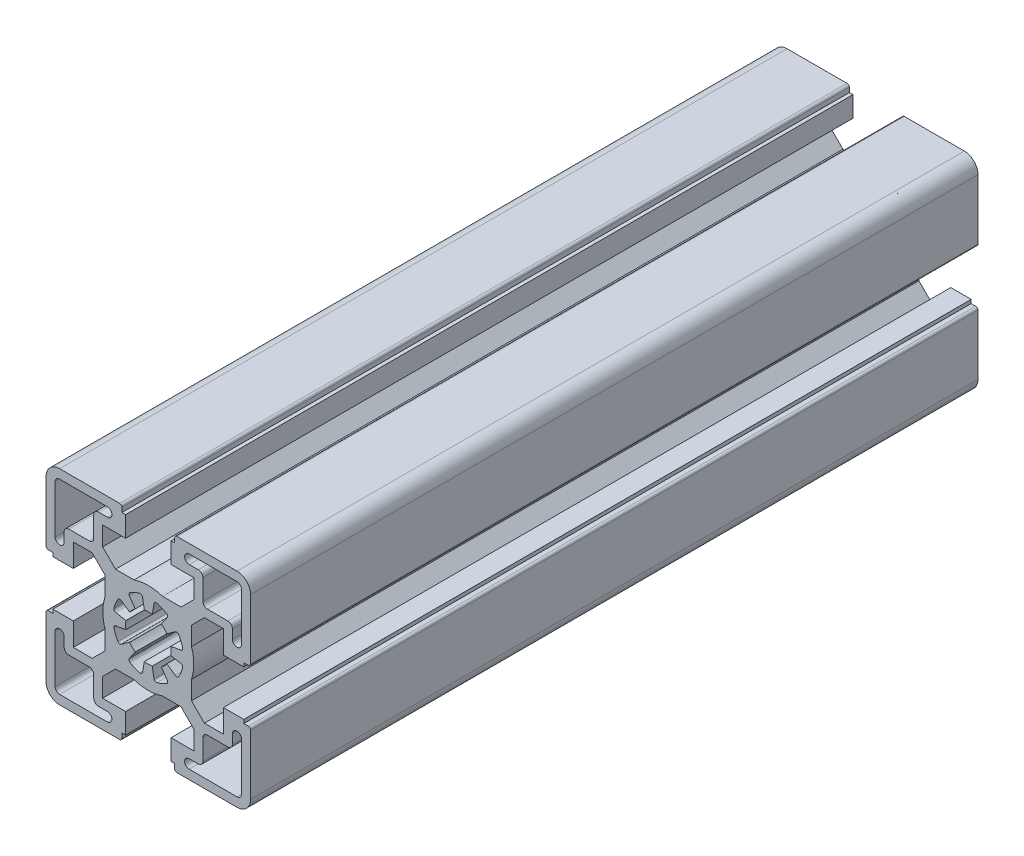
SolidWorks part; units mm, degrees
material "АД31 ГОСТ 4784-97"
ref_plane "Front Plane" through (0, 0, 0) normal (0, 0, 1) x (1, 0, 0)
ref_plane "Top Plane" through (0, 0, 0) normal (0, 1, 0) x (1, 0, 0)
ref_plane "Right Plane" through (0, 0, 0) normal (1, 0, 0) x (0, 0, -1)
sketch "Sketch1" plane through (0, 0, 0) normal (0, 0, 1) x (1, 0, 0)
  line L0 (0, 34.901) -> (0, -38.8683) construction
  line L1 (-27.7848, 0) -> (42.6814, 0) construction
  line L3 (2.8679, -4.0957) -> (4.1737, -5.9606)
  line L4 (-4.1737, -5.9606) -> (-2.8679, -4.0957)
  line L5 (-0.8682, -4.924) -> (-1.2635, -7.166)
  line L6 (0.8682, -4.924) -> (1.2636, -7.166)
  line L7 (4.0957, -2.8679) -> (5.9606, -4.1736)
  line L8 (4.924, -0.8682) -> (7.166, -1.2636)
  line L9 (-7.166, -1.2636) -> (-4.924, -0.8682)
  line L10 (-4.0957, -2.8679) -> (-5.9606, -4.1736)
  line L88 (0.8682, 4.924) -> (1.2636, 7.166)
  line L89 (-0.8682, 4.924) -> (-1.2635, 7.166)
  line L90 (-4.1737, 5.9606) -> (-2.8679, 4.0957)
  line L91 (-4.0957, 2.8679) -> (-5.9606, 4.1736)
  line L92 (-7.166, 1.2636) -> (-4.924, 0.8682)
  line L101 (4.924, 0.8682) -> (7.166, 1.2636)
  line L102 (4.0957, 2.8679) -> (5.9606, 4.1736)
  line L103 (2.8679, 4.0957) -> (4.1737, 5.9606)
  line L104 (-5, -16.4999) -> (-5, -20.9999)
  line L105 (-5, -20.9999) -> (-5.8, -20.9999)
  line L106 (-5.8, -20.9999) -> (-5.8, -22)
  line L107 (-6.3, -22.5) -> (-19.5, -22.5)
  line L108 (-22.5, -19.5) -> (-22.5, -6.2999)
  line L109 (-22, -5.7999) -> (-21, -5.7999)
  line L110 (-21, -5.7999) -> (-21, -4.9999)
  line L111 (-21, -4.9999) -> (-16.5, -4.9999)
  line L112 (-16.5, -4.9999) -> (-16.5, -10.0499)
  line L113 (-16.5, -10.0499) -> (-12.3429, -10.0499)
  line L114 (-12.3429, -10.0499) -> (-9.5, -7.207)
  line L115 (-9.5, -7.207) -> (-9.5, -3.1226)
  line L116 (-9.5, 3.1227) -> (-9.5, 7.207)
  line L117 (-9.5, 7.207) -> (-12.3429, 10.0499)
  line L118 (-12.3429, 10.0499) -> (-16.5, 10.0499)
  line L119 (-16.5, 10.0499) -> (-16.5, 4.9999)
  line L120 (-16.5, 4.9999) -> (-21, 4.9999)
  line L121 (-21, 4.9999) -> (-21, 5.7999)
  line L122 (-21, 5.7999) -> (-22, 5.7999)
  line L123 (-22.5, 6.2999) -> (-22.5, 19.5)
  line L124 (-19.5, 22.5) -> (-6.3, 22.5)
  line L125 (-5.7999, 21.9999) -> (-5.7999, 20.9999)
  line L126 (-5.7999, 20.9999) -> (-5, 20.9999)
  line L127 (-5, 20.9999) -> (-5, 16.5)
  line L128 (-5, 16.5) -> (-10.0501, 16.5)
  line L129 (-10.0501, 16.5) -> (-10.0501, 12.3428)
  line L130 (-10.0501, 12.3428) -> (-7.2072, 9.4999)
  line L131 (-7.2072, 9.4999) -> (-3.1228, 9.4999)
  line L132 (3.1226, 9.4999) -> (7.207, 9.4999)
  line L133 (7.207, 9.4999) -> (10.0499, 12.3428)
  line L134 (10.0499, 12.3428) -> (10.0499, 16.5)
  line L135 (10.0499, 16.5) -> (5, 16.5)
  line L136 (5, 16.5) -> (5, 21)
  line L137 (5, 21) -> (5.7999, 21)
  line L138 (5.7999, 21) -> (5.7999, 21.9999)
  line L139 (6.3, 22.5) -> (19.5001, 22.5)
  line L140 (22.5001, 6.2999) -> (22.5001, 19.5)
  line L141 (22.0001, 5.7999) -> (21, 5.7999)
  line L142 (21, 5.7999) -> (21, 4.9999)
  line L143 (21, 4.9999) -> (16.5, 4.9999)
  line L144 (16.5, 4.9999) -> (16.5, 10.0499)
  line L145 (16.5, 10.0499) -> (12.3429, 10.0499)
  line L146 (12.3429, 10.0499) -> (9.4999, 7.207)
  line L147 (9.4999, 7.207) -> (9.4999, 3.1227)
  line L148 (9.4999, -3.1226) -> (9.4999, -7.207)
  line L149 (9.4999, -7.207) -> (12.3429, -10.0499)
  line L150 (12.3429, -10.0499) -> (16.5, -10.0499)
  line L151 (16.5, -10.0499) -> (16.5, -4.9999)
  line L152 (16.5, -4.9999) -> (21, -4.9999)
  line L153 (21, -4.9999) -> (21, -5.7999)
  line L154 (21, -5.7999) -> (22.0001, -5.7999)
  line L155 (22.5001, -6.2999) -> (22.5001, -19.5)
  line L156 (6.3, -22.5) -> (19.5001, -22.5)
  line L157 (5.8, -22) -> (5.8, -20.9999)
  line L158 (5.8, -20.9999) -> (5, -20.9999)
  line L159 (5, -20.9999) -> (5, -16.4999)
  line L160 (5, -16.4999) -> (10.0499, -16.4999)
  line L161 (10.0499, -16.4999) -> (10.0499, -12.3428)
  line L162 (10.0499, -12.3428) -> (7.2069, -9.4998)
  line L163 (7.2069, -9.4998) -> (3.1226, -9.4998)
  line L164 (-3.1228, -9.4998) -> (-7.2071, -9.4998)
  line L165 (-7.2071, -9.4998) -> (-10.0501, -12.3428)
  line L166 (-10.0501, -12.3428) -> (-10.0501, -16.4999)
  line L167 (-10.0501, -16.4999) -> (-5, -16.4999)
  line L168 (-17.5001, -12) -> (-13.0001, -12)
  line L169 (-12.0001, -17.4999) -> (-12.0001, -13)
  line L170 (-11.0001, -18.4999) -> (-9.0001, -18.4999)
  line L171 (-19.5001, -20.5) -> (-9.0001, -20.5)
  line L172 (-20.5001, -19.5) -> (-20.5001, -8.9999)
  line L173 (-18.5001, -11) -> (-18.5001, -8.9999)
  line L174 (13, -12) -> (17.5, -12)
  line L175 (12, -17.4999) -> (12, -13)
  line L176 (9, -18.4999) -> (11, -18.4999)
  line L177 (9, -20.5) -> (19.5, -20.5)
  line L178 (20.5, -19.5) -> (20.5, -9.0001)
  line L179 (18.5, -11) -> (18.5, -9.0001)
  line L180 (-17.5001, 12) -> (-13.0001, 12)
  line L181 (-12.0001, 13) -> (-12.0001, 17.4999)
  line L182 (-11.0001, 18.4999) -> (-9.0001, 18.4999)
  line L183 (-19.5001, 20.5) -> (-9.0001, 20.5)
  line L184 (-20.5001, 8.9999) -> (-20.5001, 19.5)
  line L185 (-18.5001, 8.9999) -> (-18.5001, 11)
  line L186 (13, 12) -> (17.5, 12)
  line L187 (12, 13) -> (12, 17.4999)
  line L188 (9, 18.4999) -> (11, 18.4999)
  line L189 (9, 20.5) -> (19.5, 20.5)
  line L190 (20.5, 9.0001) -> (20.5, 19.5)
  line L191 (18.5, 9.0001) -> (18.5, 11)
  arc A0 (4.0221, -6.6756) -> (1.8763, -7.5644) centre (0, 0) cw
  arc A1 (-1.8763, -7.5645) -> (-4.0221, -6.6756) centre (0, 0) cw
  arc A2 (7.5644, -1.8763) -> (7.166, -1.2636) centre (7.0792, -1.756) ccw
  arc A3 (6.6756, -4.0221) -> (5.9606, -4.1736) centre (6.2474, -3.7641) cw
  arc A4 (4.0221, -6.6756) -> (4.1737, -5.9606) centre (3.7641, -6.2474) ccw
  arc A5 (1.8763, -7.5644) -> (1.2636, -7.166) centre (1.756, -7.0792) cw
  arc A6 (4.0957, -2.8679) -> (2.8679, -4.0957) centre (0, 0) cw
  arc A7 (7.5644, -1.8763) -> (6.6756, -4.0221) centre (0, 0) cw
  arc A8 (-1.8763, -7.5645) -> (-1.2635, -7.166) centre (-1.7559, -7.0792) ccw
  arc A9 (-4.0221, -6.6756) -> (-4.1737, -5.9606) centre (-3.7641, -6.2474) cw
  arc A10 (-6.6756, -4.0221) -> (-5.9606, -4.1736) centre (-6.2474, -3.7641) ccw
  arc A11 (-7.5644, -1.8763) -> (-7.166, -1.2636) centre (-7.0792, -1.756) cw
  arc A12 (7.166, 1.2636) -> (7.5644, 1.8763) centre (7.0792, 1.756) ccw
  arc A13 (6.6756, 4.0221) -> (5.9606, 4.1736) centre (6.2474, 3.7641) ccw
  arc A14 (4.1737, 5.9606) -> (4.0221, 6.6756) centre (3.7641, 6.2474) ccw
  arc A15 (1.8763, 7.5644) -> (1.2636, 7.166) centre (1.756, 7.0792) ccw
  arc A16 (-6.6756, -4.0221) -> (-7.5644, -1.8763) centre (0, 0) cw
  arc A17 (-2.8679, -4.0957) -> (-4.0957, -2.8679) centre (0, 0) cw
  arc A18 (0.8682, -4.924) -> (-0.8682, -4.924) centre (0, 0) cw
  arc A19 (-1.2635, 7.166) -> (-1.8763, 7.5645) centre (-1.7559, 7.0792) ccw
  arc A20 (-4.0221, 6.6756) -> (-4.1737, 5.9606) centre (-3.7641, 6.2474) ccw
  arc A21 (-7.166, 1.2636) -> (-7.5644, 1.8763) centre (-7.0792, 1.756) cw
  arc A22 (-6.6756, 4.0221) -> (-5.9606, 4.1736) centre (-6.2474, 3.7641) cw
  arc A56 (0.8682, 4.924) -> (-0.8682, 4.924) centre (0, 0) ccw
  arc A57 (-1.8763, 7.5645) -> (-4.0221, 6.6756) centre (0, 0) ccw
  arc A58 (-2.8679, 4.0957) -> (-4.0957, 2.8679) centre (0, 0) ccw
  arc A59 (-6.6756, 4.0221) -> (-7.5644, 1.8763) centre (0, 0) ccw
  arc A60 (-4.924, 0.8682) -> (-4.924, -0.8682) centre (0, 0) ccw
  arc A68 (4.924, -0.8682) -> (4.924, 0.8682) centre (0, 0) ccw
  arc A69 (7.5644, 1.8763) -> (6.6756, 4.0221) centre (0, 0) ccw
  arc A70 (4.0957, 2.8679) -> (2.8679, 4.0957) centre (0, 0) ccw
  arc A71 (4.0221, 6.6756) -> (1.8763, 7.5644) centre (0, 0) ccw
  arc A72 (-6.3, -22.5) -> (-5.8, -22) centre (-6.3, -22) ccw
  arc A73 (-22.5, -19.5) -> (-19.5, -22.5) centre (-19.5, -19.5) ccw
  arc A74 (-22, -5.7999) -> (-22.5, -6.2999) centre (-22, -6.2999) ccw
  arc A75 (-9.5, 3.1227) -> (-9.5, -3.1226) centre (0, 0.0001) ccw
  arc A76 (-22.5, 6.2999) -> (-22, 5.7999) centre (-22, 6.2999) ccw
  arc A77 (-19.5, 22.5) -> (-22.5, 19.5) centre (-19.5, 19.5) ccw
  arc A78 (-5.7999, 21.9999) -> (-6.3, 22.5) centre (-6.3, 21.9999) ccw
  arc A79 (3.1226, 9.4999) -> (-3.1228, 9.4999) centre (-0.0001, -0.0001) ccw
  arc A80 (6.3, 22.5) -> (5.7999, 21.9999) centre (6.3, 21.9999) ccw
  arc A81 (22.5001, 19.5) -> (19.5001, 22.5) centre (19.5001, 19.5) ccw
  arc A82 (22.0001, 5.7999) -> (22.5001, 6.2999) centre (22.0001, 6.2999) ccw
  arc A83 (9.4999, -3.1226) -> (9.4999, 3.1227) centre (0, 0.0001) ccw
  arc A84 (22.5001, -6.2999) -> (22.0001, -5.7999) centre (22.0001, -6.2999) ccw
  arc A85 (19.5001, -22.5) -> (22.5001, -19.5) centre (19.5001, -19.5) ccw
  arc A86 (5.8, -22) -> (6.3, -22.5) centre (6.3, -22) ccw
  arc A87 (-3.1228, -9.4998) -> (3.1226, -9.4998) centre (-0.0001, 0.0001) ccw
  arc A88 (-18.5001, -11) -> (-17.5001, -12) centre (-17.5001, -11) ccw
  arc A89 (-12.0001, -13) -> (-13.0001, -12) centre (-13.0001, -13) ccw
  arc A90 (-12.0001, -17.4999) -> (-11.0001, -18.4999) centre (-11.0001, -17.4999) ccw
  arc A91 (-9.0001, -20.5) -> (-9.0001, -18.4999) centre (-9.0001, -19.5) ccw
  arc A92 (-20.5001, -19.5) -> (-19.5001, -20.5) centre (-19.5001, -19.5) ccw
  arc A93 (-18.5001, -8.9999) -> (-20.5001, -8.9999) centre (-19.5001, -8.9999) ccw
  arc A94 (17.5, -12) -> (18.5, -11) centre (17.5, -11) ccw
  arc A95 (13, -12) -> (12, -13) centre (13, -13) ccw
  arc A96 (11, -18.4999) -> (12, -17.4999) centre (11, -17.4999) ccw
  arc A97 (9, -18.4999) -> (9, -20.5) centre (9, -19.5) ccw
  arc A98 (19.5, -20.5) -> (20.5, -19.5) centre (19.5, -19.5) ccw
  arc A99 (20.5, -9.0001) -> (18.5, -9.0001) centre (19.5, -9.0001) ccw
  arc A100 (-17.5001, 12) -> (-18.5001, 11) centre (-17.5001, 11) ccw
  arc A101 (-13.0001, 12) -> (-12.0001, 13) centre (-13.0001, 13) ccw
  arc A102 (-11.0001, 18.4999) -> (-12.0001, 17.4999) centre (-11.0001, 17.4999) ccw
  arc A103 (-9.0001, 18.4999) -> (-9.0001, 20.5) centre (-9.0001, 19.5) ccw
  arc A104 (-19.5001, 20.5) -> (-20.5001, 19.5) centre (-19.5001, 19.5) ccw
  arc A105 (-20.5001, 8.9999) -> (-18.5001, 8.9999) centre (-19.5001, 8.9999) ccw
  arc A106 (18.5, 11) -> (17.5, 12) centre (17.5, 11) ccw
  arc A107 (12, 13) -> (13, 12) centre (13, 13) ccw
  arc A108 (12, 17.4999) -> (11, 18.4999) centre (11, 17.4999) ccw
  arc A109 (9, 20.5) -> (9, 18.4999) centre (9, 19.5) ccw
  arc A110 (20.5, 19.5) -> (19.5, 20.5) centre (19.5, 19.5) ccw
  arc A111 (18.5, 9.0001) -> (20.5, 9.0001) centre (19.5, 9.0001) ccw
  dimension "D5" = 10
  dimension "D7" = 0.5
  dimension "D1" = 45.0001
  dimension "D2" = 44.9999
  dimension "D3" = 12.5001
  dimension "D4" = 10
  dimension "D6" = 22.5001
extrude "Base-Extrude" add sketch "Sketch1" along normal blind 160
